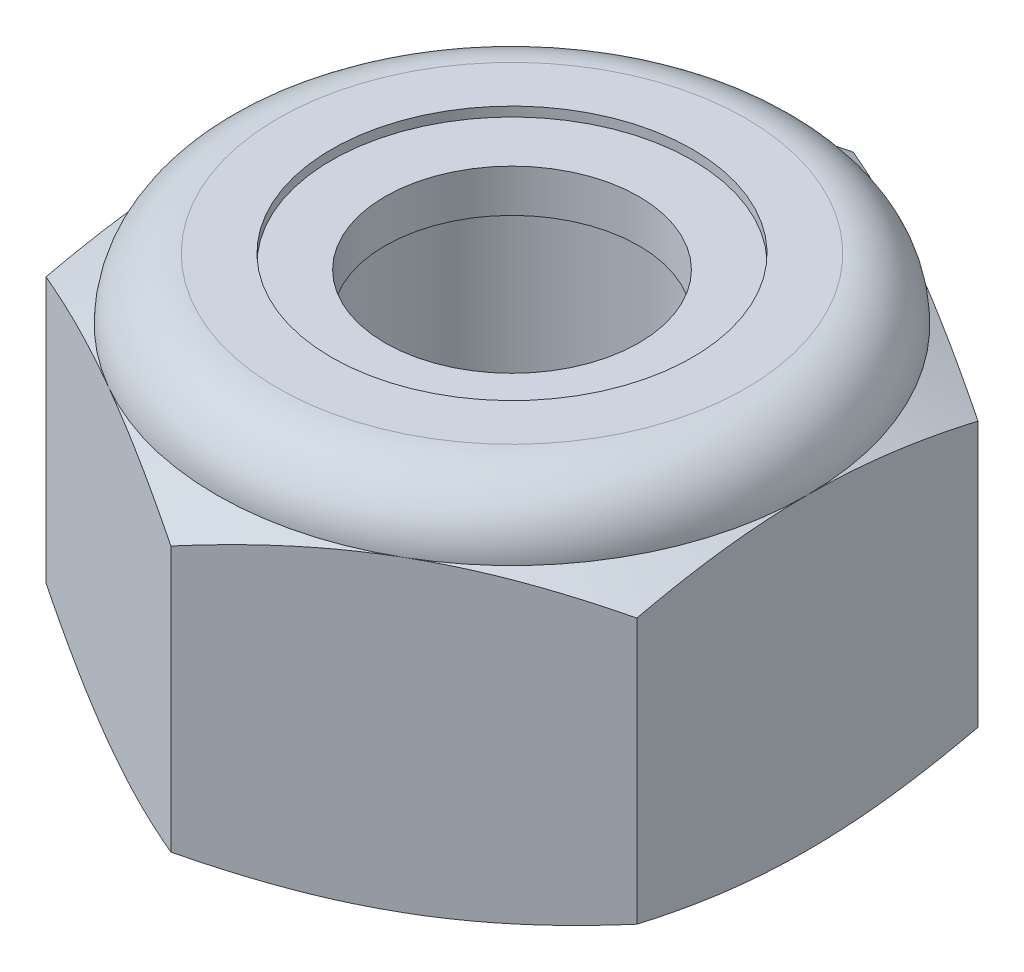
SolidWorks part; units mm, degrees
ref_plane "Front" through (0, 0, 0) normal (0, 0, 1) x (1, 0, 0)
ref_plane "Top" through (0, 0, 0) normal (0, 1, 0) x (1, 0, 0)
ref_plane "Right" through (0, 0, 0) normal (1, 0, 0) x (0, 0, -1)
sketch "Sketch1" plane through (0, 0, 0) normal (0, 1, 0) x (1, 0, 0)
  line L1 (0, 5.4993) -> (-4.7625, 2.7496)
  line L2 (-4.7625, 2.7496) -> (-4.7625, -2.7496)
  line L3 (-4.7625, -2.7496) -> (0, -5.4993)
  line L4 (0, -5.4993) -> (4.7625, -2.7496)
  line L5 (4.7625, -2.7496) -> (4.7625, 2.7496)
  line L6 (4.7625, 2.7496) -> (0, 5.4993)
  circle A0 centre (0, 0) radius 4.7625 construction
  dimension "Hex Flats" = 9.525
extrude "Extrude1" add sketch "Sketch1" along normal blind 5.9531
sketch "Sketch2" plane through (0, 0, 0) normal (1, 0, 0) x (0, 0, -1)
  line L0 (-2.413, 0) -> (-2.413, 5.9531) construction
  line L1 (0, 0) -> (2.413, 0)
  line L2 (0, 0) -> (0, 5.9531)
  line L3 (0, 5.9531) -> (2.413, 5.9531)
  line L4 (2.413, 0) -> (2.413, 5.9531)
  line L5 (-2.7496, 5.9531) -> (2.7496, 5.9531) construction
  line L7 (0, -2.413) -> (0, 0) construction
  dimension "Thread Dia" = 4.826
revolve "Revolve1" add sketch "Sketch2" angle 360 about L7
sketch "Sketch3" plane through (0, 0, 0) normal (1, 0, 0) x (0, 0, -1)
  line L0 (2.413, 5.9531) -> (-2.413, 5.9531) construction
  line L1 (-2.413, 5.9531) -> (-2.413, 5.1594) construction
  line L2 (-2.413, 5.1594) -> (2.413, 5.9531) construction
  line L3 (2.413, 5.9531) -> (2.4291, 5.8552) construction
  line L4 (2.4291, 5.8552) -> (2.5418, 5.1699)
  line L5 (2.5418, 5.1699) -> (2.0776, 5.3449)
  line L6 (2.0776, 5.3449) -> (2.0454, 5.5407)
  line L7 (2.0454, 5.5407) -> (2.4291, 5.8552)
  line L8 (2.0615, 5.4428) -> (2.4855, 5.5126) construction
  line L9 (2.413, 5.9531) -> (2.413, 5.5006) construction
  line L10 (2.413, 5.5006) -> (-2.413, 4.7069) construction
  line L11 (-2.413, 4.7069) -> (-2.413, 5.1594) construction
  line L12 (-0.1397, 5.9531) -> (0.1397, 4.2544) construction
  line L13 (-2.413, 0) -> (-2.413, 5.9531) construction
  line L14 (0, 5.9531) -> (2.413, 5.9531) construction
  line L15 (2.413, 0) -> (2.413, 5.9531) construction
  point P13 (0, 5.1038)
  dimension "D1" = 0.0992
  dimension "D2" = 0.1984
  dimension "Thread Pitch" = 0.7937
  dimension "D4" = 60
  dimension "D5" = 0.7937
revolve "Cut-Revolve1" [suppressed] cut sketch "Sketch3" angle 360 about L12
pattern_linear "LPattern1" [suppressed] count 8 spacing 0.7937 along (0, 1, 0) count 2 spacing 0.7937 along (0, 1, 0)
sketch "Sketch4" plane through (0, 0, 0) normal (1, 0, 0) x (0, 0, -1)
  line L0 (0, 5.9531) -> (2.413, 5.9531)
  line L1 (2.413, 5.9531) -> (2.0454, 5.7817)
  line L2 (2.0454, 5.7817) -> (2.0454, 0.1714)
  line L3 (2.0454, 0.1714) -> (2.413, 0)
  line L4 (2.413, 0) -> (0, 0)
  line L5 (0, 0) -> (0, 5.9531)
  line L6 (2.413, 0) -> (2.413, 5.9531) construction
  line L7 (0, 5.9531) -> (2.413, 5.9531) construction
  line L8 (0, 0) -> (2.413, 0) construction
  line L9 (0, 0) -> (0, 5.9531) construction
  line L10 (0, 5.9531) -> (0, 6.3587) construction
  dimension "D1" = 25
revolve "Cut-Revolve2" cut sketch "Sketch4" angle 360 about L10
combine bodies "Combine1" operation type subtract main body 112 bodies to subtract 109
sketch "Sketch5" plane through (0, 0, 0) normal (1, 0, 0) x (0, 0, -1)
  line L0 (0, 0) -> (4.7625, 0)
  line L1 (4.7625, 0) -> (5.4993, 0.3436)
  line L2 (5.4993, 0.3436) -> (5.4993, 4.6174)
  line L3 (5.4993, 4.6174) -> (4.7625, 4.9609)
  line L4 (3.7703, 5.9531) -> (3.7703, 7.2231)
  line L5 (3.7703, 7.2231) -> (6.7693, 7.2231)
  line L6 (6.7693, 7.2231) -> (6.7693, -1.27)
  line L7 (6.7693, -1.27) -> (0, -1.27)
  line L8 (0, -1.27) -> (0, 0)
  line L9 (4.7625, 4.9609) -> (4.7625, 0) construction
  line L10 (0, 0) -> (2.413, 0) construction
  line L13 (5.4993, 2.4805) -> (6.7693, 2.4805) construction
  line L14 (5.4993, 5.9531) -> (5.4993, 0) construction
  line L15 (0, 0) -> (0, 7.2231) construction
  line L20 (0, 7.2231) -> (3.7703, 7.2231) construction
  line L22 (0, 5.9531) -> (2.413, 5.9531) construction
  arc A0 (4.7625, 4.9609) -> (3.7703, 5.9531) centre (3.7703, 4.9609) ccw
  dimension "D1" = 25
  dimension "D2" = 1.27
  dimension "D3" = 5.9531
  dimension "D4" = 0.9922
revolve "Cut-Revolve3" cut sketch "Sketch5" angle 360 about L15
sketch "Sketch6" plane through (0, 0, 0) normal (1, 0, 0) x (0, 0, -1)
  line L0 (0, 4.9609) -> (4.6101, 4.9609)
  line L1 (3.7703, 5.8007) -> (2.9079, 5.8007)
  line L2 (0, 7.2231) -> (0, 4.9609)
  line L3 (2.9079, 7.2231) -> (0, 7.2231)
  line L4 (0, 7.2231) -> (3.7703, 7.2231) construction
  line L5 (0, 0) -> (0, 7.2231) construction
  line L6 (0, 7.2231) -> (0, 44.323) construction
  line L7 (2.9079, 5.8007) -> (2.9079, 7.2231)
  line L8 (3.7703, 5.9531) -> (3.7703, 5.8007) construction
  line L9 (2.9079, 5.8007) -> (2.0454, 5.8007) construction
  line L10 (2.0454, 5.8007) -> (2.0454, 5.7817) construction
  arc A0 (4.6101, 4.9609) -> (3.7703, 5.8007) centre (3.7703, 4.9609) ccw
  arc A1 (4.7625, 4.9609) -> (3.7703, 5.9531) centre (3.7703, 4.9609) ccw construction
  dimension "D1" = 0.1524
revolve "Cut-Revolve4" cut sketch "Sketch6" angle 360 about L6
sketch "Sketch7" plane through (0, 0, 0) normal (1, 0, 0) x (0, 0, -1)
  line L0 (2.0454, 5.0371) -> (4.5301, 5.0371)
  line L1 (3.7703, 5.7245) -> (2.0454, 5.7245)
  line L2 (2.0454, 5.7245) -> (2.0454, 5.0371)
  line L3 (2.0454, 5.0371) -> (0, 5.0371) construction
  line L4 (0, 5.0371) -> (0, 5.7245) construction
  line L5 (0, 5.7245) -> (2.0454, 5.7245) construction
  line L6 (2.0454, 5.0371) -> (2.0454, 4.9609) construction
  line L7 (0, 4.9609) -> (4.6101, 4.9609) construction
  line L8 (3.7703, 5.7245) -> (3.7703, 5.8007) construction
  arc A0 (4.5301, 5.0371) -> (3.7703, 5.7245) centre (3.7703, 4.9609) ccw
  arc A2 (4.6101, 4.9609) -> (3.7703, 5.8007) centre (3.7703, 4.9609) ccw construction
  dimension "D1" = 0.0762
revolve "Revolve2" add sketch "Sketch7" angle 360 about L4
equation "\"D1@Sketch3\"=\"Thread Pitch@Sketch3\"/8"
equation "\"D2@Sketch3\"=\"Thread Pitch@Sketch3\"/4"
equation "\"D5@Sketch3\"=\"Thread Pitch@Sketch3\""
equation "\"D4@LPattern1\"=\"Thread Pitch@Sketch3\""
equation "\"D3@LPattern1\"=\"Thread Pitch@Sketch3\""
equation "\"D1@LPattern1\"=\"Height@Extrude1\"/\"Thread Pitch@Sketch3\""
equation "\"D4@Sketch5\"=\"Height@Extrude1\"/6"
